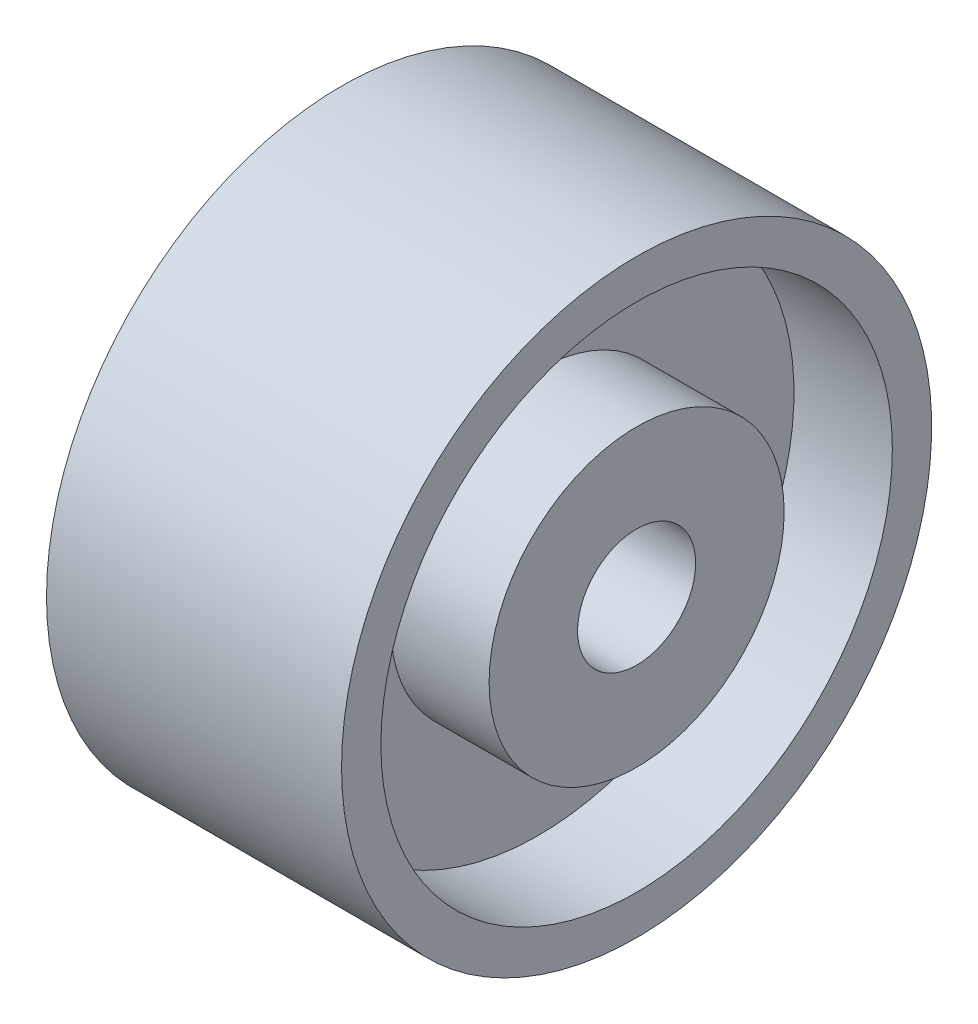
SolidWorks part; units mm, degrees
ref_plane "Ön Düzlem" through (0, 0, 0) normal (0, 0, 1) x (1, 0, 0)
ref_plane "Üst Düzlem" through (0, 0, 0) normal (0, 1, 0) x (1, 0, 0)
ref_plane "Sağ Düzlem" through (0, 0, 0) normal (1, 0, 0) x (0, 0, -1)
sketch "Çizim1" plane through (0, 0, 0) normal (1, 0, 0) x (0, 0, -1)
  circle A0 centre (0, 0) radius 15
extrude "Yükseklik-Ekstrüzyon1" add sketch "Çizim1" along normal blind 30
sketch "Çizim2" plane through (0, 0, 0) normal (-1, 0, 0) x (0, 0, 1)
  circle A0 centre (0, 0) radius 10
extrude "Kes-Ekstrüzyon2" cut sketch "Çizim2" against normal blind 30
sketch "Çizim13" plane through (0, 0, 0) normal (-1, 0, 0) x (0, 0, 1)
  circle A0 centre (0, 0) radius 30
extrude "Yükseklik-Ekstrüzyon3" add sketch "Çizim13" against normal blind 30
sketch "Çizim14" plane through (0, 0, 0) normal (-1, 0, 0) x (0, 0, 1)
  circle A0 centre (0, 0) radius 26
extrude "Kes-Ekstrüzyon3" cut sketch "Çizim14" against normal blind 15
sketch "Çizim15" plane through (0, 0, 0) normal (-1, 0, 0) x (0, 0, 1)
  circle A0 centre (0, 0) radius 15
extrude "Yükseklik-Ekstrüzyon4" add sketch "Çizim15" along normal blind 15 and the other way blind 15
sketch "Çizim16" plane through (-15, 0, 0) normal (-1, 0, 0) x (0, 0, 1)
  circle A0 centre (0, 0) radius 10
extrude "Kes-Ekstrüzyon5" cut sketch "Çizim16" against normal blind 45
sketch "Çizim17" plane through (30, 0, 0) normal (1, 0, 0) x (0, 0, -1)
  circle A0 centre (0, 0) radius 26
extrude "Kes-Ekstrüzyon8" cut sketch "Çizim17" against normal blind 15 and the other way through all
ref_plane "Düzlem1" through (15, 0, 0) normal (-1, 0, 0) x (0, 0, 1)
sketch "Çizim19" plane through (15, 0, 0) normal (-1, 0, 0) x (0, 0, 1)
  circle A0 centre (0, 0) radius 26
extrude "Yükseklik-Ekstrüzyon5" add sketch "Çizim19" along normal blind 5 and the other way blind 5
sketch "Çizim20" plane through (20, 0, 0) normal (1, 0, 0) x (0, 0, -1)
  circle A0 centre (0, 0) radius 15
extrude "Yükseklik-Ekstrüzyon6" add sketch "Çizim20" along normal blind 10
sketch "Çizim21" plane through (-15, 0, 0) normal (-1, 0, 0) x (0, 0, 1)
  circle A0 centre (0, 0) radius 10
extrude "Kes-Ekstrüzyon9" cut sketch "Çizim21" against normal blind 55
sketch "Çizim24" plane through (-15, 0, 0) normal (-1, 0, 0) x (0, 0, 1)
  circle A0 centre (0, 0) radius 15
extrude "Kes-Ekstrüzyon10" cut sketch "Çizim24" against normal blind 15
sketch "Çizim25" plane through (10, 0, 0) normal (-1, 0, 0) x (0, 0, 1)
  circle A2 centre (0, 0) radius 19
sketch "Çizim26" plane through (0, 0, 0) normal (1, 0, 0) x (0, 0, -1)
  circle A0 centre (0, 0) radius 10
  circle A1 centre (0, 0) radius 6
  dimension "D1" = 12
extrude "Yükseklik-Ekstrüzyon7" add sketch "Çizim26" along normal up to surface (30 mm away) up to face at (30, 0, -10)
